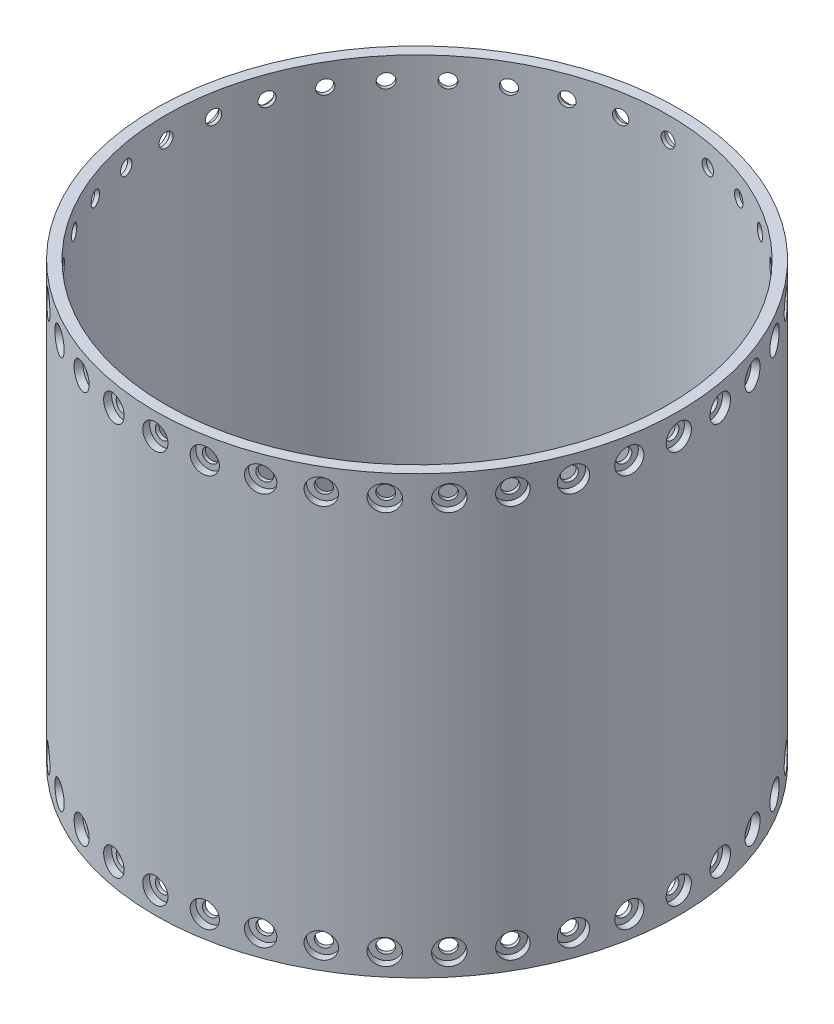
SolidWorks part; units mm, degrees
material "6061-T6 (SS)"
ref_plane "Front Plane" through (0, 0, 0) normal (0, 0, 1) x (1, 0, 0)
ref_plane "Top Plane" through (0, 0, 0) normal (0, 1, 0) x (1, 0, 0)
ref_plane "Right Plane" through (0, 0, 0) normal (1, 0, 0) x (0, 0, -1)
sketch "Sketch1" plane through (0, 0, 0) normal (0, 1, 0) x (1, 0, 0)
  circle A0 centre (0, 0) radius 152.4
  circle A1 centre (0, 0) radius 146.05
  dimension "D1" = 304.8
  dimension "D2" = 6.35
extrude "Boss-Extrude1" add sketch "Sketch1" along normal blind 254
ref_plane "Plane1" through (-152.4, 0, 0) normal (-1, 0, 0) x (0, 0, 1)
hole_wizard "CBORE for 5/16 Button Head Cap Screw1" positions "Sketch2" profile "Sketch4" counterbore size "5/16" standard "ANSI Inch"
sketch "Sketch2" plane through (-152.4, 0, 0) normal (-1, 0, 0) x (0, 0, 1)
  line L0 (0, 241.3) -> (0, 0) construction
  line L2 (146.05, 254) -> (-146.05, 254) construction
  point P0 (0, 241.3)
  dimension "D1" = 12.7
sketch "Sketch4" plane through (-152.4, 241.3, 0) normal (0, 1, 0) x (0, 0, 1)
  line L0 (0, 0) -> (0, 121.0828)
  line L1 (0, 121.0828) -> (4.1021, 118.618)
  line L2 (4.1021, 118.618) -> (4.1021, 4.2164)
  line L3 (4.1021, 4.2164) -> (7.3419, 4.2164)
  line L4 (7.3419, 4.2164) -> (7.3419, 0)
  line L5 (7.3419, 0) -> (0, 0)
  line L10 (0, 121.0828) -> (-4.1021, 118.618) construction
  line L11 (0, -6.35) -> (0, 107.95) construction
  dimension "Hole Dia." = 8.2042
  dimension "Hole Depth" = 118.618
  dimension "C'Bore Dia." = 14.6837
  dimension "C'Bore Depth" = 4.2164
  dimension "Drill Angle" = 118
pattern_circular "CirPattern1" count 36 over 360 about axis through (0, 0, 0) along (0, 1, 0) of "CBORE for 5/16 Button Head Cap Screw1"
ref_plane "Plane2" through (0, 127, 0) normal (0, 1, 0) x (1, 0, 0)
mirror "Mirror1" about plane through (0, 127, 0) normal (0, 1, 0) of "CirPattern1", "CBORE for 5/16 Button Head Cap Screw1"
